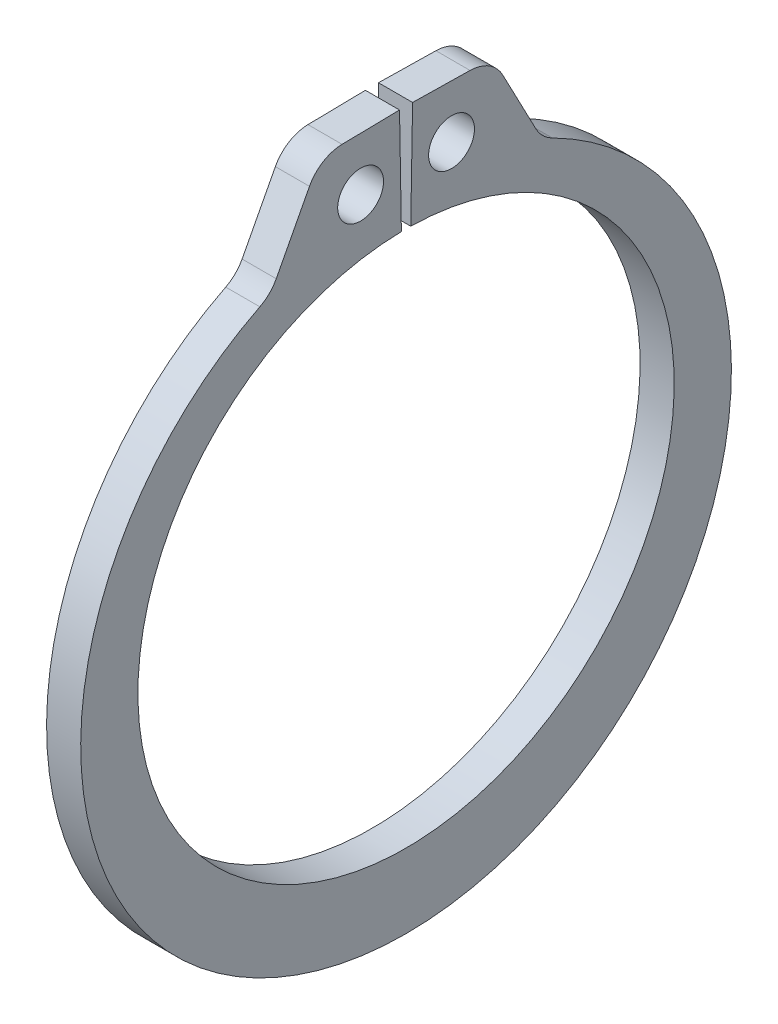
SolidWorks part; units mm, degrees
material "Cast Carbon Steel"
ref_plane "Front" through (0, 0, 0) normal (0, 0, 1) x (1, 0, 0)
ref_plane "Top" through (0, 0, 0) normal (0, 1, 0) x (1, 0, 0)
ref_plane "Right" through (0, 0, 0) normal (1, 0, 0) x (0, 0, -1)
sketch "Sketch1" plane through (0, 0, 0) normal (1, 0, 0) x (0, 0, -1)
  line L0 (0, 0) -> (0, 6.985) construction
  line L1 (-0.1219, 6.9839) -> (-0.1702, 9.7521)
  line L2 (0.1702, 9.7521) -> (2.2464, 9.7159)
  line L3 (2.2464, 9.7159) -> (3.5321, 7.264)
  line L4 (0.1219, 6.9839) -> (0.1702, 9.7521)
  line L5 (-0.1702, 9.7521) -> (-2.2464, 9.7159)
  line L6 (-2.2464, 9.7159) -> (-3.5321, 7.264)
  line L7 (-3.5321, 7.264) -> (-3.0545, 6.2817) construction
  line L8 (3.5321, 7.264) -> (3.0545, 6.2817) construction
  line L9 (0, -6.985) -> (0, -8.9154) construction
  line L10 (-2.2464, 9.7159) -> (-0.1219, 6.9839) construction
  line L11 (0, 6.985) -> (0, 9.7536) construction
  line L12 (-6.985, 0) -> (6.985, 0) construction
  circle A0 centre (0, 0) radius 6.985 construction
  arc A1 (-0.1219, 6.9839) -> (0.1219, 6.9839) centre (0, 0) ccw
  circle A3 centre (0, 0) radius 10.7315 construction
  circle A4 centre (-1.1841, 8.3499) radius 0.5969
  circle A5 centre (1.1841, 8.3499) radius 0.5969
  arc A6 (-3.5321, 7.264) -> (3.5321, 7.264) centre (0, -0.4402) ccw
  point P0 (0, -8.9154)
  dimension "A" = 13.97
  dimension "Hole" = 1.1938
  dimension "Smin" = 1.0922
  dimension "H" = 2.7686
  dimension "D2" = 2.0764
  dimension "Angle" = 1
extrude "Extrude1" add sketch "Sketch1" along normal mid plane 0.889
fillet "Fillet1" radius 0.9779 4 edges at (0, 7.264, 3.5321) (0, 7.264, -3.5321) (0, 9.7159, 2.2464) (0, 9.7159, -2.2464)
sketch "Sketch2" plane through (0, 0, 0) normal (0, 0, 1) x (1, 0, 0)
  line L0 (-4.9403, 0) -> (12.8397, 0)
  line L1 (12.8397, 0) -> (12.8397, -7.5438)
  line L2 (-0.4953, -7.5438) -> (-4.4958, -7.5438)
  line L3 (12.8397, -7.5438) -> (0.4953, -7.5438)
  line L4 (0.4953, -7.5438) -> (0.4953, -7.0993)
  line L5 (0.4953, -7.0993) -> (-0.4953, -7.0993)
  line L6 (-0.4953, -7.0993) -> (-0.4953, -7.5438)
  line L7 (-0.4953, -7.5438) -> (-4.9403, -7.5438) construction
  line L8 (-4.9403, -7.5438) -> (-4.9403, 0) construction
  line L9 (12.8397, 0) -> (76.391, 0) construction
  line L10 (-4.4958, -7.5438) -> (-4.9403, -7.0993)
  line L11 (-4.9403, -7.0993) -> (-4.9403, 0)
  point P10 (0, -7.0993)
  dimension "D2" = 17.78
  dimension "D3" = 4.445
  dimension "D1" = 45
revolve "Revolve1" [suppressed] add sketch "Sketch2" angle 360 about L9
delete or keep bodies "Body-Delete1" [suppressed] type delete bodies bodies 122
equation "\"D2@Sketch2\" = \"D1@Extrude1\"*20"
equation "\"D3@Sketch2\" = \"D2@Sketch2\"/4"
equation "\"D2@Sketch1\" = \"H@Sketch1\"*.75"
